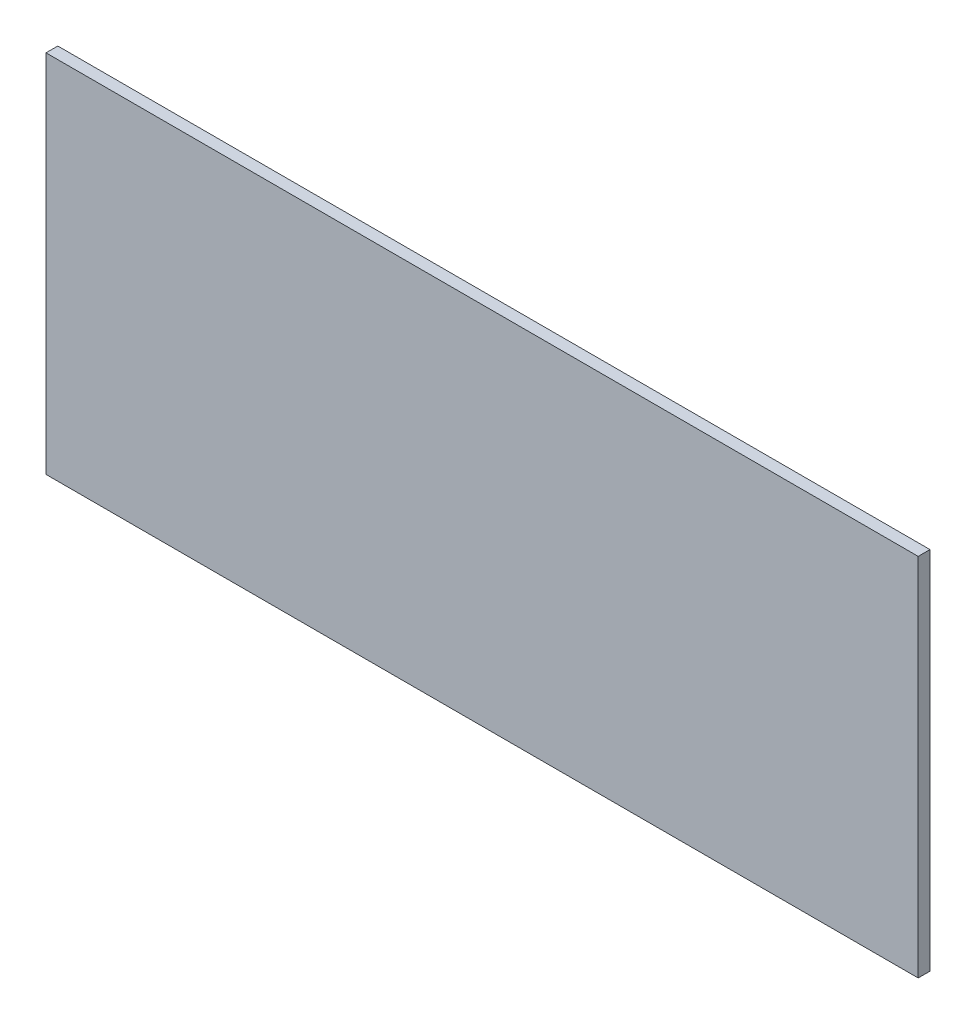
SolidWorks part; units mm, degrees
material "Plain Carbon Steel"
ref_plane "Front Plane" through (0, 0, 0) normal (0, 0, 1) x (1, 0, 0)
ref_plane "Top Plane" through (0, 0, 0) normal (0, 1, 0) x (1, 0, 0)
ref_plane "Right Plane" through (0, 0, 0) normal (1, 0, 0) x (0, 0, -1)
sketch "Sketch1" plane through (0, 0, 0) normal (0, 0, 1) x (1, 0, 0)
  line L1 (0, 0) -> (112.268, 0)
  line L2 (0, 0) -> (0, 47)
  line L3 (0, 47) -> (112.268, 47)
  line L4 (112.268, 0) -> (112.268, 47)
  dimension "D1" = 112.268
  dimension "D2" = 47
extrude "Boss-Extrude1" add sketch "Sketch1" along normal blind 1.5189
